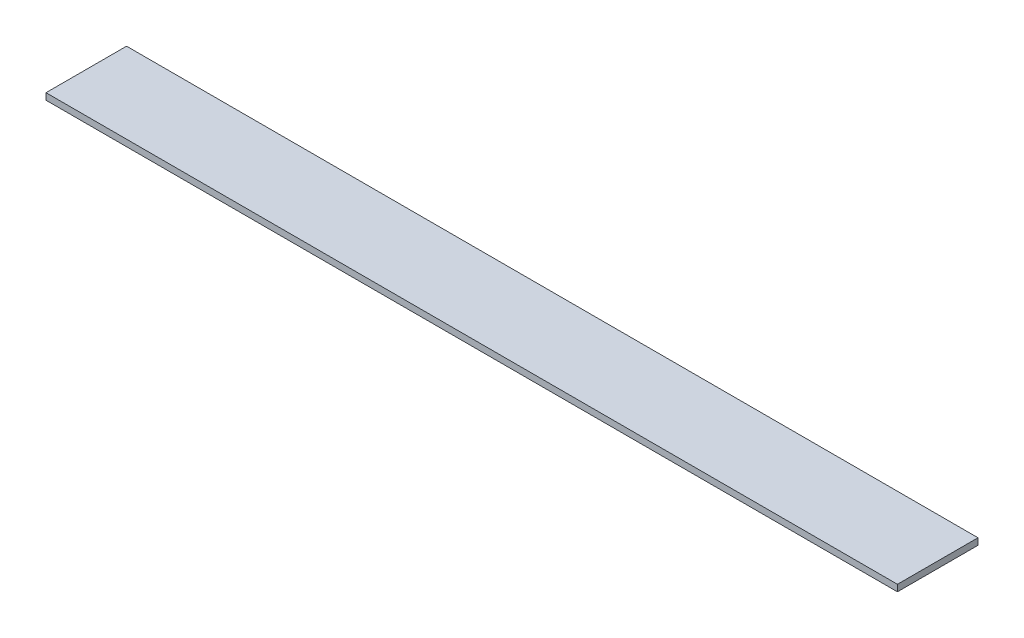
SolidWorks part; units mm, degrees
ref_plane "Front Plane" through (0, 0, 0) normal (0, 0, 1) x (1, 0, 0)
ref_plane "Top Plane" through (0, 0, 0) normal (0, 1, 0) x (1, 0, 0)
ref_plane "Right Plane" through (0, 0, 0) normal (1, 0, 0) x (0, 0, -1)
sketch "Sketch1" plane through (0, 0, 0) normal (0, 1, 0) x (1, 0, 0)
  line L1 (0, 0) -> (130, 0)
  line L2 (0, 0) -> (0, 12.3)
  line L3 (0, 12.3) -> (130, 12.3)
  line L4 (130, 0) -> (130, 12.3)
  dimension "D1" = 12.3
  dimension "D2" = 130
extrude "Boss-Extrude1" add sketch "Sketch1" along normal blind 1
